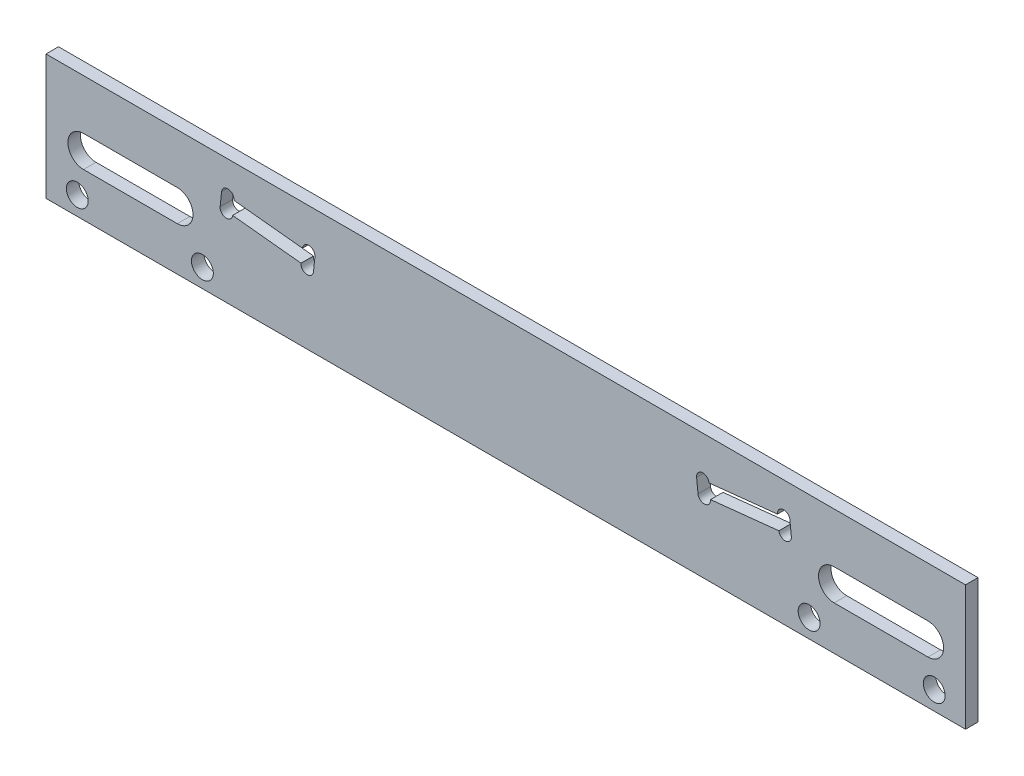
SolidWorks part; units mm, degrees
ref_plane "前视基准面" through (0, 0, 0) normal (0, 0, 1) x (1, 0, 0)
ref_plane "上视基准面" through (0, 0, 0) normal (0, 1, 0) x (1, 0, 0)
ref_plane "右视基准面" through (0, 0, 0) normal (1, 0, 0) x (0, 0, -1)
sketch "草图1" plane through (0, 0, 0) normal (0, 0, 1) x (1, 0, 0)
  line L1 (-73.5, 10) -> (73.5, 10)
  line L2 (-73.5, 10) -> (-73.5, -10)
  line L3 (-73.5, -10) -> (73.5, -10)
  line L4 (73.5, 10) -> (73.5, -10)
  line L5 (-73.5, 10) -> (73.5, -10) construction
  line L6 (-73.5, -10) -> (73.5, 10) construction
  point P0 (0, 0)
  dimension "D1" = 147
  dimension "D2" = 20
extrude "凸台-拉伸1" add sketch "草图1" along normal blind 2
sketch "草图2" plane through (0, 0, 2) normal (0, 0, 1) x (1, 0, 0)
  line L0 (30.5109, 3.397) -> (30.7409, 1.209)
  line L1 (30.7409, 1.209) -> (45.6587, 2.777)
  line L2 (45.6587, 2.777) -> (45.4287, 4.9649)
  line L3 (45.4287, 4.9649) -> (30.5109, 3.397)
  line L4 (73.5, 10) -> (-73.5, 10) construction
  dimension "D1" = 45.6587
  dimension "D2" = 2.777
  dimension "D3" = 2.2
  dimension "D4" = 15
  dimension "D5" = 6
extrude "切除-拉伸1" cut sketch "草图2" against normal blind 3
sketch "草图3" plane through (0, 0, 2) normal (0, 0, 1) x (1, 0, 0)
  line L1 (45.4287, 4.9649) -> (30.5109, 3.397) construction
  line L2 (30.7409, 1.209) -> (45.6587, 2.777) construction
  line L3 (45.6587, 2.777) -> (45.4287, 4.9649) construction
  line L4 (30.5109, 3.397) -> (30.7409, 1.209) construction
  circle A4 centre (31.5054, 3.5015) radius 1
  circle A5 centre (31.7354, 1.3136) radius 1
  circle A6 centre (44.4342, 4.8604) radius 1
  circle A7 centre (44.6642, 2.6724) radius 1
  dimension "D1" = 2
extrude "切除-拉伸2" cut sketch "草图3" against normal through all
mirror "镜向1" about plane through (0, 0, 0) normal (1, 0, 0) of "切除-拉伸2", "切除-拉伸1"
sketch "草图4" plane through (0, 0, 0) normal (0, 0, -1) x (-1, 0, 0)
  circle A0 centre (68.5, -7) radius 1.75
  circle A1 centre (48.5, -7) radius 1.75
  circle A2 centre (-48.5, -7) radius 1.75
  circle A3 centre (-68.5, -7) radius 1.75
  dimension "D1" = 3.5
extrude "切除-拉伸3" cut sketch "草图4" against normal through all
sketch "草图5" plane through (0, 0, 2) normal (0, 0, 1) x (1, 0, 0)
  line L0 (52.5, -0.5) -> (67.5, -0.5) construction
  line L1 (52.5, 2) -> (67.5, 2)
  line L2 (52.5, -3) -> (67.5, -3)
  line L3 (-73.5, -10) -> (73.5, -10) construction
  arc A0 (52.5, 2) -> (52.5, -3) centre (52.5, -0.5) ccw
  arc A1 (67.5, -3) -> (67.5, 2) centre (67.5, -0.5) ccw
  point P2 (60, -0.5)
  dimension "D3" = 2.5
  dimension "D1" = 60
  dimension "D2" = 15
  dimension "D4" = 7
extrude "切除-拉伸4" cut sketch "草图5" against normal through all
mirror "镜向2" about plane through (0, 0, 0) normal (1, 0, 0) of "切除-拉伸4"
